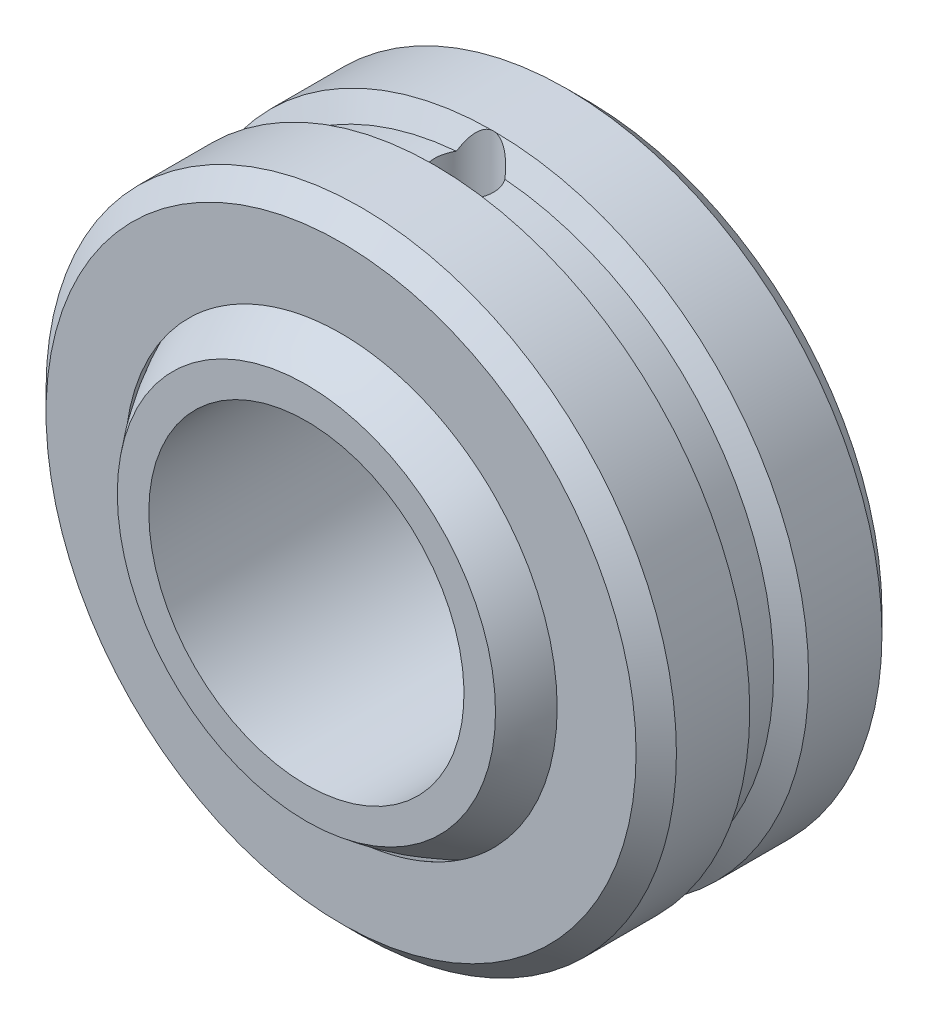
SolidWorks part; units mm, degrees
ref_plane "Front" through (0, 0, 0) normal (0, 0, 1) x (1, 0, 0)
ref_plane "Top" through (0, 0, 0) normal (0, 1, 0) x (1, 0, 0)
ref_plane "Right" through (0, 0, 0) normal (1, 0, 0) x (0, 0, -1)
sketch "Sketch1" plane through (0, 0, 0) normal (0, 0, 1) x (1, 0, 0)
  circle A0 centre (0, 0) radius 6.35 construction
  circle A1 centre (0, 0) radius 9.9187 construction
  circle A2 centre (0, 0) radius 10.0179 construction
  circle A3 centre (0, 0) radius 12.7
  dimension "D OD" = 25.4
  dimension "B Hole Dia" = 12.7
  dimension "Ball Dia" = 19.8374
  dimension "D1" = 20.0358
extrude "Extrude1" add sketch "Sketch1" along normal mid plane 9.906
sketch "Sketch2" plane through (0, 0, 0) normal (0, 0, 1) x (1, 0, 0)
  line L0 (0, 10.0179) -> (0, -10.0179)
  line L1 (0, 10.0179) -> (0, 12.7) construction
  circle A0 centre (0, 0) radius 10.0179 construction
  arc A1 (0, -10.0179) -> (0, 10.0179) centre (0, 0) ccw
  circle A2 centre (0, 0) radius 12.7 construction
revolve "Cut-Revolve1" cut sketch "Sketch2" angle 360 about L1
sketch "Sketch3" plane through (0, 0, 0) normal (0, 0, 1) x (1, 0, 0)
  line L0 (0, 9.9187) -> (0, -9.9187)
  line L1 (0, 9.9187) -> (0, 12.7) construction
  circle A0 centre (0, 0) radius 9.9187 construction
  arc A1 (0, -9.9187) -> (0, 9.9187) centre (0, 0) ccw
  circle A2 centre (0, 0) radius 12.7 construction
revolve "Revolve1" add sketch "Sketch3" angle 360 about L1
sketch "Sketch4" plane through (0, 0, 0) normal (0, 0, 1) x (1, 0, 0)
  circle A0 centre (0, 0) radius 6.35 construction
  circle A1 centre (0, 0) radius 6.35
extrude "Cut-Extrude1" cut sketch "Sketch4" against normal through all and the other way through all
sketch "Sketch5" plane through (0, 0, 0) normal (1, 0, 0) x (0, 0, -1)
  line L0 (-6.35, 12.7) -> (6.35, 12.7) construction
  line L1 (-6.35, 12.7) -> (-7.6196, 12.7)
  line L2 (-6.35, 12.7) -> (-6.35, -12.7)
  line L3 (-6.35, -12.7) -> (-7.6196, -12.7)
  line L4 (-7.6196, 12.7) -> (-7.6196, -12.7)
  line L5 (6.35, -12.7) -> (7.6196, -12.7)
  line L6 (6.35, -12.7) -> (6.35, 12.7)
  line L7 (6.35, 12.7) -> (7.6196, 12.7)
  line L8 (7.6196, -12.7) -> (7.6196, 12.7)
  line L16 (4.953, 12.7) -> (-4.953, 12.7) construction
  line L17 (7.6196, -6.35) -> (7.6196, 6.35) construction
  line L18 (-7.6196, -6.35) -> (-7.6196, 6.35) construction
  line L19 (-6.35, -12.7) -> (6.35, -12.7) construction
  line L20 (-4.953, -12.7) -> (4.953, -12.7) construction
  line L21 (0, 0) -> (-6.35, 1.0626) construction
  line L22 (0, 0) -> (-6.35, -1.0626) construction
  dimension "W ball Width" = 12.7
  dimension "Mis Angle" = 19
extrude "Cut-Extrude2" cut sketch "Sketch5" against normal through all and the other way through all
chamfer "Chamfer1" distance 0.8128 angle 45 2 edges at (12.7, 0, 4.953) (12.7, 0, -4.953)
sketch "Sketch6" plane through (0, 0, 0) normal (1, 0, 0) x (0, 0, -1)
  line L0 (-1.1867, 12.7) -> (-0.6705, 11.806)
  line L1 (-0.6705, 11.806) -> (0.6705, 11.806)
  line L2 (0.6705, 11.806) -> (1.1867, 12.7)
  line L3 (-1.1867, 12.7) -> (1.1867, 12.7)
  line L4 (4.1402, 12.7) -> (-4.1402, 12.7) construction
  line L5 (0, 0) -> (0, 11.806) construction
  line L6 (0, 0) -> (6.35, 0) construction
  line L7 (6.35, -7.6196) -> (6.35, 7.6196) construction
  line L8 (0, 10.0179) -> (0, 12.7) construction
  arc A0 (4.953, 8.7078) -> (-4.953, 8.7078) centre (0, 0) ccw construction
  dimension "D1" = 60
  dimension "D2" = 2.6821
  dimension "D3" = 0.894
  dimension "D4" = 1.3411
revolve "Cut-Revolve2" cut sketch "Sketch6" angle 360 about L6
sketch "Sketch8" plane through (0, 0, 0) normal (0, 1, 0) x (1, 0, 0)
  circle A0 centre (0, 0) radius 1.1867
extrude "Cut-Extrude3" cut sketch "Sketch8" along normal through all
sketch "Sketch7" plane through (0, 0, 0) normal (1, 0, 0) x (0, 0, -1)
  line L0 (0, 0) -> (-6.35, -1.0626) construction
  line L1 (0, 0) -> (-6.35, 1.0626) construction
  line L2 (0, 0) -> (-6.35, -1.0626) construction
  line L3 (0, 0) -> (-6.35, 1.0626) construction
equation "\"D1@Sketch1\"=\"Ball Dia@Sketch1\"*1.01"
equation "\"D3@Sketch6\" = \"D2@Sketch6\"/3"
equation "\"D4@Sketch6\" = \"D3@Sketch6\"*1.5"
